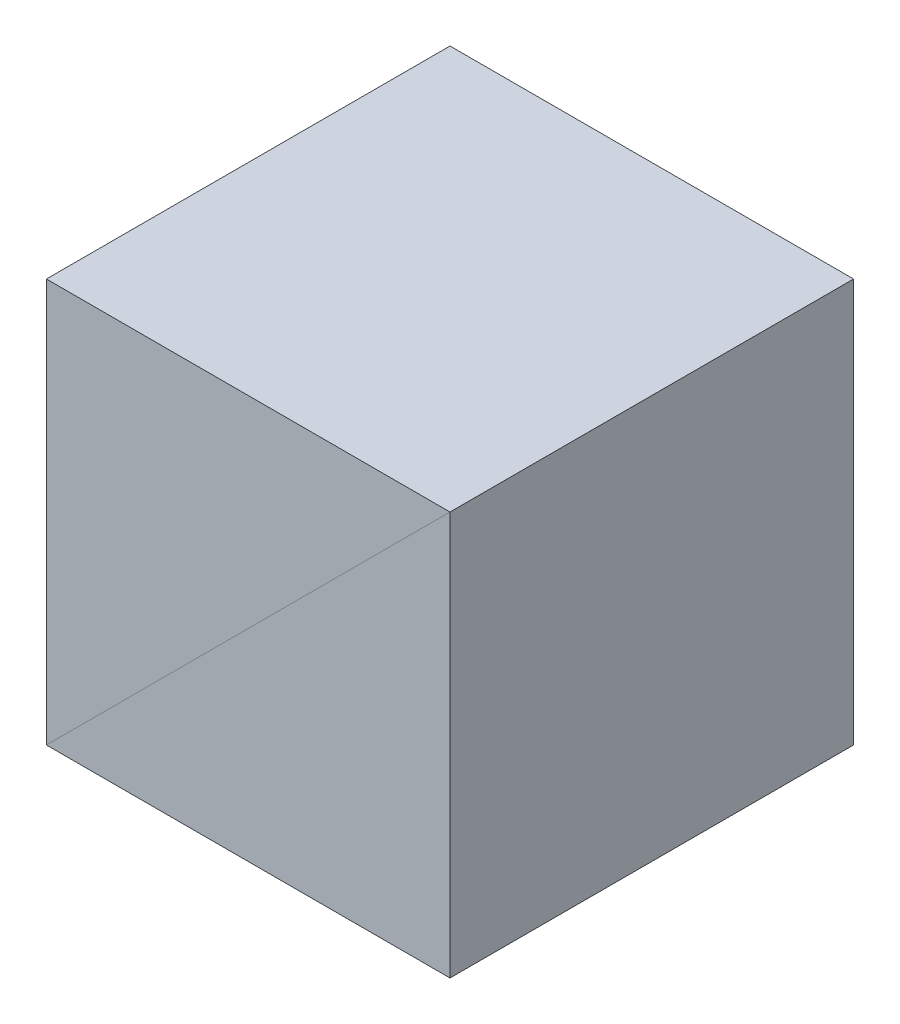
SolidWorks part; units mm, degrees
ref_plane "前视基准面" through (0, 0, 0) normal (0, 0, 1) x (1, 0, 0)
ref_plane "上视基准面" through (0, 0, 0) normal (0, 1, 0) x (1, 0, 0)
ref_plane "右视基准面" through (0, 0, 0) normal (1, 0, 0) x (0, 0, -1)
sketch "草图1" plane through (0, 0, 0) normal (0, 0, 1) x (1, 0, 0)
  line L3 (-2.5, -2.5) -> (2.5, -2.5)
  line L4 (2.5, 2.5) -> (2.5, -2.5)
  line L5 (2.5, 2.5) -> (-2.5, -2.5)
  dimension "D1" = 5
extrude "凸台-拉伸1" add sketch "草图1" along normal mid plane 5
mirror "镜向2" about plane through (2.5, 2.5, 2.5) normal (0.7071, -0.7071, 0) of bodies 107
